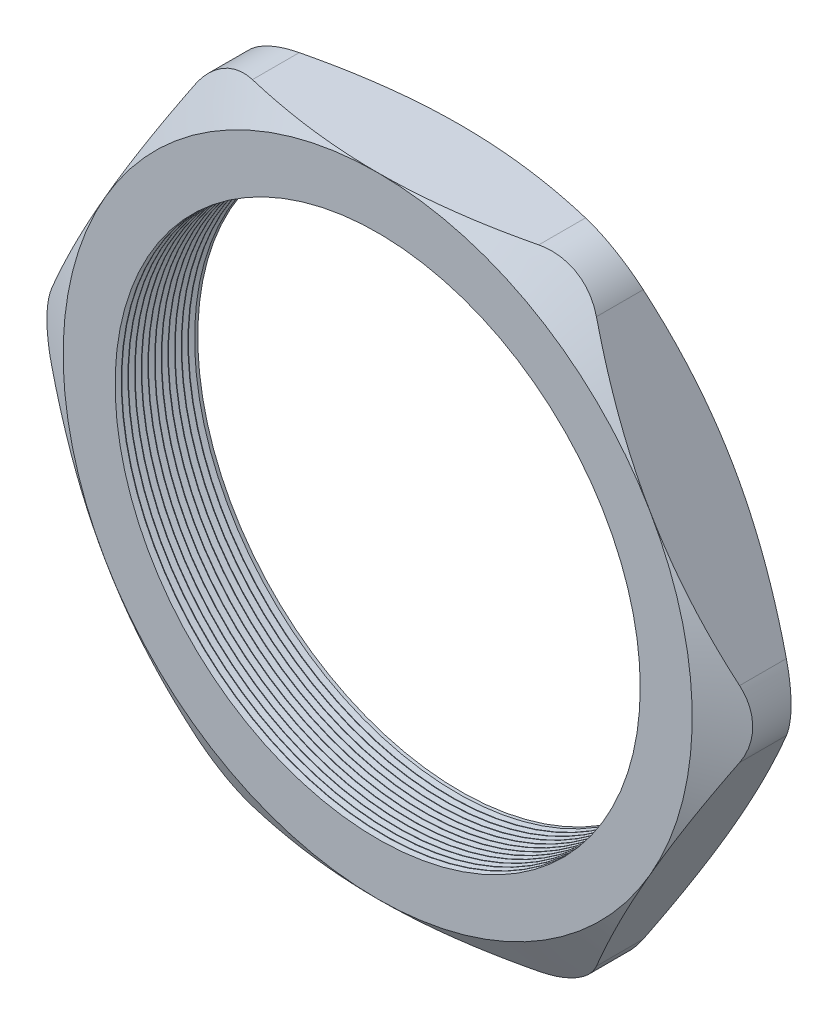
SolidWorks part; units mm, degrees
ref_plane "Front Plane" through (0, 0, 0) normal (0, 0, 1) x (1, 0, 0)
ref_plane "Top Plane" through (0, 0, 0) normal (0, 1, 0) x (1, 0, 0)
ref_plane "Right Plane" through (0, 0, 0) normal (1, 0, 0) x (0, 0, -1)
sketch "Sketch1" plane through (0, 0, 0) normal (0, 0, 1) x (1, 0, 0)
  line L1 (-34.6087, 0) -> (-17.3043, -29.972)
  line L2 (-17.3043, -29.972) -> (17.3043, -29.972)
  line L3 (17.3043, -29.972) -> (34.6087, 0)
  line L4 (34.6087, 0) -> (17.3043, 29.972)
  line L5 (17.3043, 29.972) -> (-17.3043, 29.972)
  line L6 (-17.3043, 29.972) -> (-34.6087, 0)
  circle A0 centre (0, 0) radius 29.972 construction
  circle A1 centre (0, 0) radius 25.019
  dimension "TS" = 50.038
  dimension "H" = 59.944
extrude "Extrude1" add sketch "Sketch1" along normal blind 7.874
sketch "Sketch2" plane through (0, 0, 7.874) normal (0, 0, 1) x (1, 0, 0)
  line L0 (17.3043, 29.972) -> (-17.3043, 29.972) construction
  circle A0 centre (0, 0) radius 29.972
extrude "Cut-Extrude1" cut sketch "Sketch2" against normal through all draft 60 flip side to cut
sketch "Sketch3" plane through (0, 0, 0) normal (0, 0, -1) x (-1, 0, 0)
  line L0 (-17.3043, 29.972) -> (17.3043, 29.972) construction
  circle A0 centre (0, 0) radius 29.972
extrude "Cut-Extrude2" cut sketch "Sketch3" against normal through all draft 60 flip side to cut
fillet "Fillet1" radius 6.35 6 edges at (34.6087, 0, 3.937) (17.3043, -29.972, 3.937) (-17.3043, -29.972, 3.937) (-34.6087, 0, 3.937) (-17.3043, 29.972, 3.937) (17.3043, 29.972, 3.937)
sketch "Sketch4" plane through (0, 0, 0) normal (0, 1, 0) x (1, 0, 0)
  line L0 (-25.019, -7.874) -> (-25.019, -7.2874)
  line L1 (-25.019, 0) -> (-25.019, -7.874) construction
  line L2 (-25.019, -7.2874) -> (-25.527, -7.5807)
  line L3 (-25.527, -7.5807) -> (-25.019, -7.874)
  dimension "D1" = 60
  dimension "D2" = 60
  dimension "D3" = 0.508
revolve "Cut-Revolve1" cut sketch "Sketch4" angle 360 about axis through (0, 0, 0) along (0, 0, 1)
pattern_linear "LPattern1" count 12 spacing 0.635 along (0, 0, -1) of "Cut-Revolve1"
